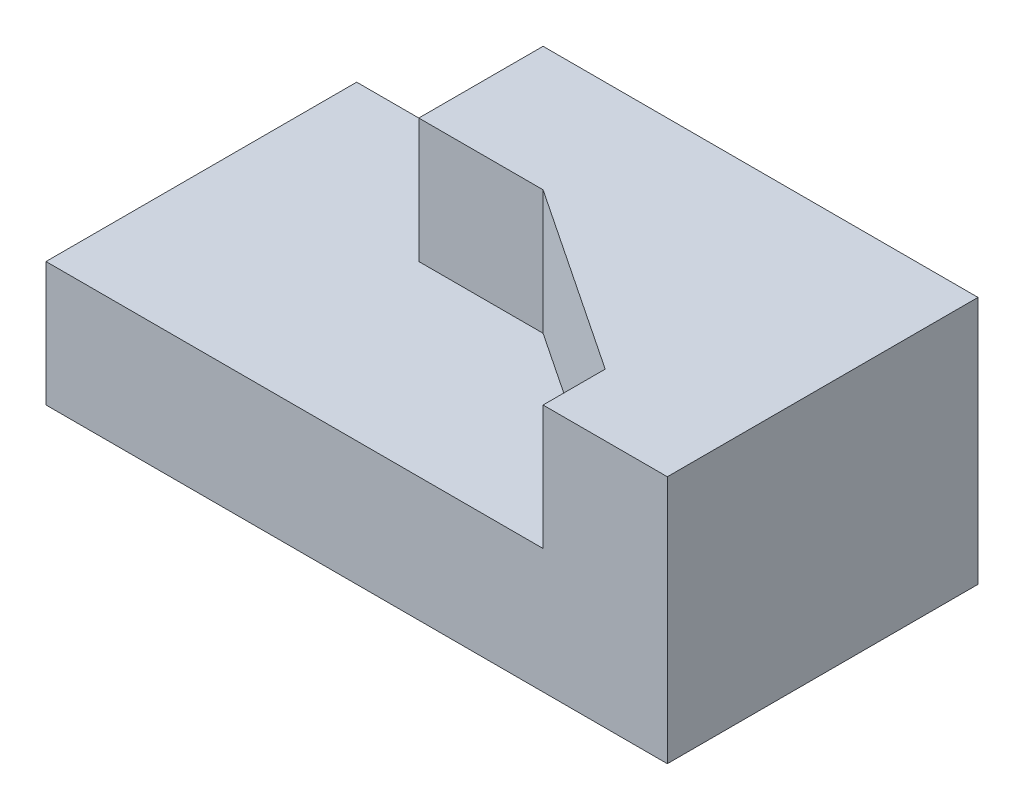
SolidWorks part; units mm, degrees
ref_plane "Front Plane" through (0, 0, 0) normal (0, 0, 1) x (1, 0, 0)
ref_plane "Top Plane" through (0, 0, 0) normal (0, 1, 0) x (1, 0, 0)
ref_plane "Right Plane" through (0, 0, 0) normal (1, 0, 0) x (0, 0, -1)
sketch "Sketch1" plane through (0, 0, 0) normal (0, 1, 0) x (1, 0, 0)
  line L1 (0, 0) -> (100, 0)
  line L2 (0, 0) -> (0, 50)
  line L3 (0, 50) -> (100, 50)
  line L4 (100, 0) -> (100, 50)
  dimension "D1" = 50
  dimension "D2" = 100
extrude "Boss-Extrude1" add sketch "Sketch1" along normal blind 20
sketch "Sketch2" plane through (0, 20, 0) normal (0, 1, 0) x (1, 0, 0)
  line L0 (30, 50) -> (30, 30)
  line L1 (100, 50) -> (0, 50) construction
  line L2 (30, 30) -> (50, 30)
  line L3 (50, 30) -> (80, 10)
  line L4 (80, 10) -> (80, 0)
  line L5 (0, 0) -> (100, 0) construction
  line L6 (80, 0) -> (100, 0)
  line L7 (100, 0) -> (100, 50)
  line L8 (100, 50) -> (30, 50)
  dimension "D1" = 70
  dimension "D2" = 20
  dimension "D3" = 10
  dimension "D4" = 20
  dimension "D5" = 20
extrude "Boss-Extrude2" add sketch "Sketch2" along normal blind 20
